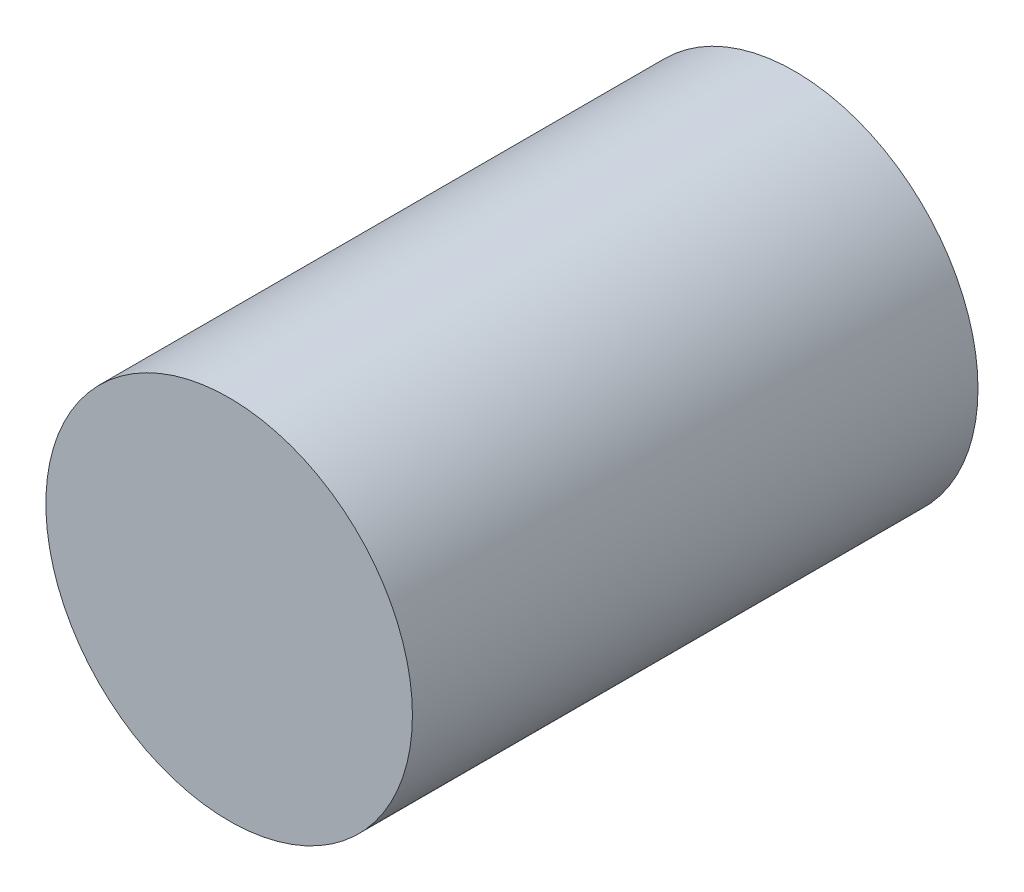
SolidWorks part; units mm, degrees
ref_plane "Front Plane" through (0, 0, 0) normal (0, 0, 1) x (1, 0, 0)
ref_plane "Top Plane" through (0, 0, 0) normal (0, 1, 0) x (1, 0, 0)
ref_plane "Right Plane" through (0, 0, 0) normal (1, 0, 0) x (0, 0, -1)
sketch "Sketch1" plane through (0, 0, 0) normal (0, 0, 1) x (1, 0, 0)
  circle A0 centre (0, 0) radius 16.4465
  dimension "D1" = 32.893
extrude "Extrude1" add sketch "Sketch1" along normal blind 50.7492
